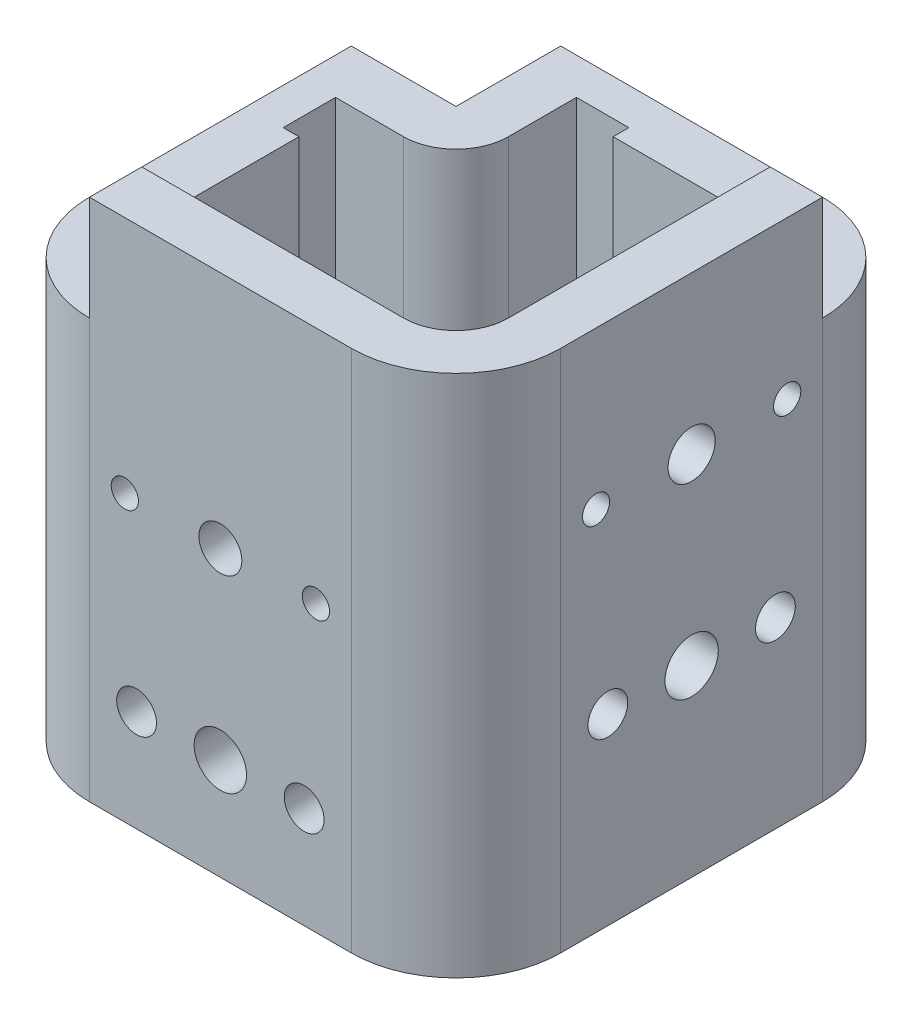
SolidWorks part; units mm, degrees
material "ABS"
ref_plane "Front Plane" through (0, 0, 0) normal (0, 0, 1) x (1, 0, 0)
ref_plane "Top Plane" through (0, 0, 0) normal (0, 1, 0) x (1, 0, 0)
ref_plane "Right Plane" through (0, 0, 0) normal (1, 0, 0) x (0, 0, -1)
sketch "Sketch1" plane through (0, 0, 0) normal (0, 1, 0) x (1, 0, 0)
  line L1 (-25, 35) -> (25, 35)
  line L2 (-35, 25) -> (-35, -25)
  line L3 (-25, -35) -> (25, -35)
  line L4 (35, 25) -> (35, -25)
  line L5 (-25, -25) -> (25, 25) construction
  line L6 (-25, 25) -> (25, -25) construction
  line L7 (-25, 45) -> (25, 45)
  line L8 (45, 25) -> (45, -25)
  line L9 (-25, -45) -> (25, -45)
  line L10 (-45, 25) -> (-45, -25)
  arc A0 (35, 25) -> (25, 35) centre (25, 25) ccw
  arc A1 (25, -35) -> (35, -25) centre (25, -25) ccw
  arc A2 (-35, -25) -> (-25, -35) centre (-25, -25) ccw
  arc A3 (-35, 25) -> (-25, 35) centre (-25, 25) cw
  arc A5 (45, 25) -> (25, 45) centre (25, 25) ccw
  arc A6 (25, -45) -> (45, -25) centre (25, -25) ccw
  arc A7 (-45, -25) -> (-25, -45) centre (-25, -25) ccw
  arc A8 (-45, 25) -> (-25, 45) centre (-25, 25) cw
  point P12 (0, 0)
  dimension "D1" = 10
  dimension "D3" = 10
  dimension "D2" = 70
extrude "Boss-Extrude1" add sketch "Sketch1" along normal blind 30 and the other way blind 70
sketch "Sketch2" plane through (45, 0, 0) normal (1, 0, 0) x (0, 0, -1)
  arc A2 (20.8484, 0) -> (15.6484, 0) centre (18.2484, 0) ccw construction
  circle A3 centre (-0.0016, 0) radius 4.5 construction
  circle A4 centre (-0.0016, -35) radius 5.1 construction
  circle A5 centre (-0.0016, 0) radius 4.5
  circle A6 centre (-0.0016, -35) radius 5.1
  arc A7 (15.6484, 0) -> (20.8484, 0) centre (18.2484, 0) ccw construction
  arc A8 (-15.6516, 0) -> (-20.8516, 0) centre (-18.2516, 0) ccw construction
  arc A9 (-20.8516, 0) -> (-15.6516, 0) centre (-18.2516, 0) ccw construction
  arc A10 (20.8484, 0) -> (15.6484, 0) centre (18.2484, 0) ccw
  arc A11 (15.6484, 0) -> (20.8484, 0) centre (18.2484, 0) ccw
  arc A12 (-15.6516, 0) -> (-20.8516, 0) centre (-18.2516, 0) ccw
  arc A13 (-20.8516, 0) -> (-15.6516, 0) centre (-18.2516, 0) ccw
  circle A14 centre (15.9984, -35) radius 3.8 construction
  circle A15 centre (-16.0016, -35) radius 3.8 construction
  circle A16 centre (15.9984, -35) radius 3.8
  circle A17 centre (-16.0016, -35) radius 3.8
extrude "Cut-Extrude1" cut sketch "Sketch2" against normal up to next
sketch "Sketch5" plane through (45, 0, 0) normal (1, 0, 0) x (0, 0, -1)
  line L0 (25, 30) -> (25, -70) construction
  line L1 (25, 10) -> (45, 10)
  line L2 (25, 10) -> (25, 30)
  line L3 (25, 30) -> (45, 30)
  line L4 (45, 10) -> (45, 30)
  line L5 (-25, 30) -> (25, 30) construction
  line L6 (45, 30) -> (45, -70) construction
  dimension "D1" = 20
extrude "Cut-Extrude2" cut sketch "Sketch5" against normal through all
sketch "Sketch7" plane through (0, 0, 45) normal (0, 0, 1) x (1, 0, 0)
  line L0 (-25, -70) -> (-25, 30) construction
  line L1 (-25, 10) -> (-45, 10)
  line L2 (-25, 10) -> (-25, 30)
  line L3 (-25, 30) -> (-45, 30)
  line L4 (-45, 10) -> (-45, 30)
  line L5 (-25, 30) -> (25, 30) construction
  line L6 (-45, -70) -> (-45, 30) construction
  dimension "D1" = 20
extrude "Cut-Extrude3" cut sketch "Sketch7" against normal up to next
sketch "Sketch8" plane through (0, 0, 45) normal (0, 0, 1) x (1, 0, 0)
  line L0 (0, 30) -> (0, -70) construction
  line L1 (-25, 30) -> (25, 30) construction
  line L2 (-25, -70) -> (25, -70) construction
  circle A0 centre (640, -50.6) radius 5 construction
  circle A1 centre (640, -15.6) radius 5 construction
  circle A2 centre (640, -50.6) radius 5
  circle A3 centre (640, -15.6) radius 5
  circle A4 centre (0, -15.6) radius 4.1
  circle A5 centre (0, -50.6) radius 5
  circle A7 centre (640, -50.6) radius 5 construction
  circle A8 centre (-16, -50.6) radius 3.8 construction
  circle A9 centre (16, -50.6) radius 3.8 construction
  circle A10 centre (-16, -50.6) radius 3.8
  circle A11 centre (16, -50.6) radius 3.8
  arc A12 (-15.65, -15.6) -> (-20.85, -15.6) centre (-18.25, -15.6) ccw construction
  arc A13 (-20.85, -15.6) -> (-15.65, -15.6) centre (-18.25, -15.6) ccw construction
  arc A14 (20.85, -15.6) -> (15.65, -15.6) centre (18.25, -15.6) ccw construction
  arc A15 (15.65, -15.6) -> (20.85, -15.6) centre (18.25, -15.6) ccw construction
  arc A16 (-15.65, -15.6) -> (-20.85, -15.6) centre (-18.25, -15.6) ccw
  arc A17 (-20.85, -15.6) -> (-15.65, -15.6) centre (-18.25, -15.6) ccw
  arc A18 (20.85, -15.6) -> (15.65, -15.6) centre (18.25, -15.6) ccw
  arc A19 (15.65, -15.6) -> (20.85, -15.6) centre (18.25, -15.6) ccw
  dimension "D1" = 8.2
extrude "Cut-Extrude6" cut sketch "Sketch8" against normal up to surface (10 mm away) up to face at (-5, -14, 35)
sketch "Sketch9" plane through (0, 10, 0) normal (0, 1, 0) x (1, 0, 0)
  line L0 (-45, 25) -> (-45, -25) construction
  line L1 (-25, 45) -> (25, 45) construction
  line L2 (-25, 25) -> (-45, 25)
  line L3 (-25, 25) -> (-25, 45)
  line L4 (-25, 45) -> (-45, 45)
  line L5 (-45, 25) -> (-45, 45)
  line L6 (675, 4.9984) -> (678, 4.9984) construction
  line L7 (-35, 25) -> (-38, 25)
  line L8 (-35, 25) -> (-35, 5)
  line L9 (-35, 5) -> (-38, 5)
  line L10 (-38, 25) -> (-38, 5)
  line L11 (-25, 35) -> (-5, 35)
  line L12 (-25, 35) -> (-25, 38)
  line L13 (-25, 38) -> (-5, 38)
  line L14 (-5, 35) -> (-5, 38)
  line L16 (-35, -25) -> (-35, 25) construction
  arc M5 (-25, 45) -> (-45, 25) centre (-25, 25) ccw
  line M6 (-45, 25) -> (-45, -25)
  line M10 (-35, -25) -> (-35, 25)
  arc M11 (-35, 25) -> (-25, 35) centre (-25, 25) cw
  line M12 (-25, 35) -> (25, 35)
  line M16 (25, 45) -> (-25, 45)
  dimension "D1" = 20
  dimension "D2" = 20
extrude "Cut-Extrude7" cut sketch "Sketch9" against normal through all contours L2 L10 L9 M10 | L10 L7 L3 L2 M11 M12 M16 M5 M6 | L14 L13 L3 M12
sketch "Sketch10" plane through (0, 10, 0) normal (0, 1, 0) x (1, 0, 0)
  line L0 (-25, 45) -> (-25, 25)
  line L1 (-45, 25) -> (-25, 25)
  line L3 (-45, 15) -> (-25, 15)
  line L4 (-15, 45) -> (-15, 25)
  line L5 (-45, 15) -> (-15, 15) construction
  line L6 (-15, 45) -> (-15, 15) construction
  line L7 (-45, 25) -> (-25, 25) construction
  line L8 (-45, 25) -> (-45, -25) construction
  line L9 (-25, 45) -> (-25, 25) construction
  line L10 (-25, 45) -> (25, 45) construction
  line L11 (-15, 45) -> (-25, 45)
  line L12 (-45, 25) -> (-45, 15)
  arc A0 (-25, 15) -> (-15, 25) centre (-25, 25) ccw
  dimension "D2" = 10
  dimension "D1" = 10
extrude "Boss-Extrude2" add sketch "Sketch10" against normal up to surface (80 mm away) up to face at (-3.9893, -70, -3.9893)
